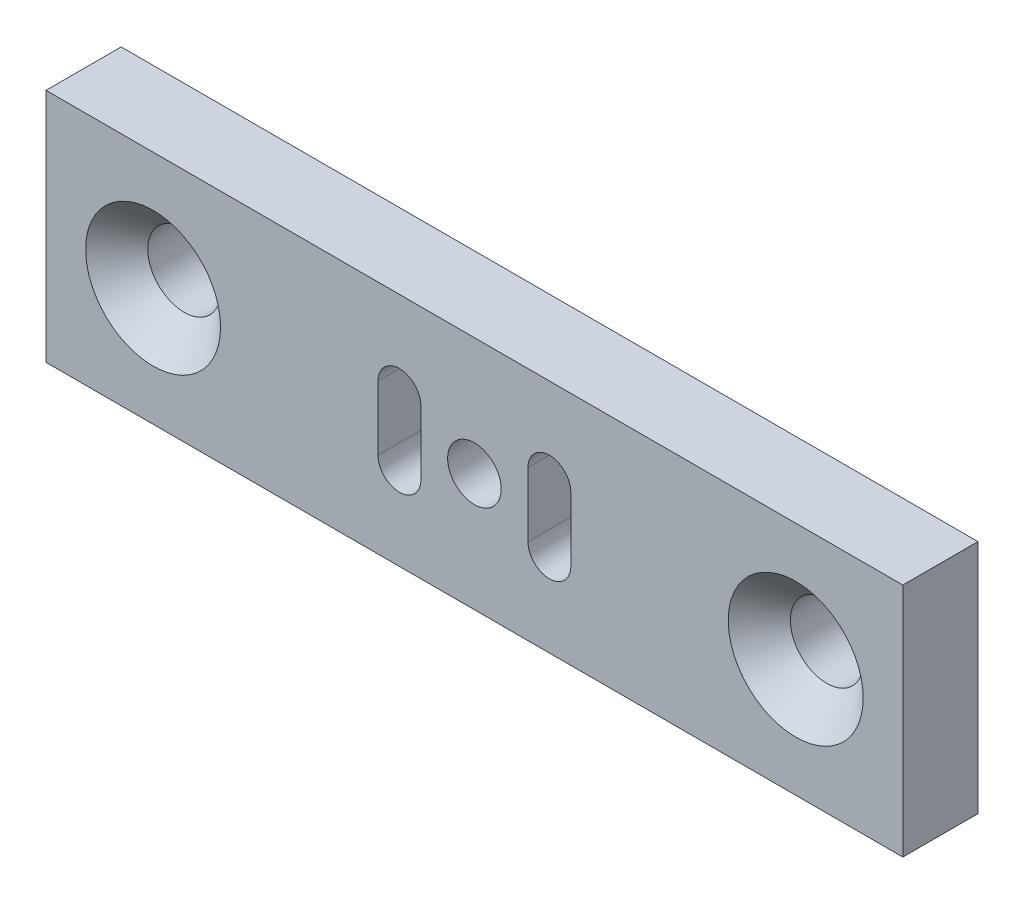
SolidWorks part; units mm, degrees
ref_plane "Plan de face" through (0, 0, 0) normal (0, 0, 1) x (1, 0, 0)
ref_plane "Plan de dessus" through (0, 0, 0) normal (0, 1, 0) x (1, 0, 0)
ref_plane "Plan de droite" through (0, 0, 0) normal (1, 0, 0) x (0, 0, -1)
sketch "Esquisse1" plane through (0, 0, 0) normal (0, 0, 1) x (1, 0, 0)
  line L0 (-2.625, 3.0182) -> (-2.625, -3.0182) construction
  line L1 (2.625, 3.0182) -> (-2.625, 3.0182) construction
  line L2 (2.625, 3.0182) -> (2.625, -3.0182) construction
  line L3 (2.625, -3.0182) -> (-2.625, -3.0182) construction
  line L5 (2.625, 3.0182) -> (-2.625, -3.0182) construction
  line L6 (2.625, -3.0182) -> (-2.625, 3.0182) construction
  line L8 (-4.341, -1.1938) -> (-20, -5.5) construction
  line L9 (20, -5.5) -> (-20, -5.5)
  line L10 (20, -5.5) -> (20, 5.5)
  line L11 (20, 5.5) -> (-20, 5.5)
  line L12 (-20, -5.5) -> (-20, 5.5)
  line L13 (20, -5.5) -> (-20, 5.5) construction
  line L14 (20, 5.5) -> (0, 0) construction
  circle A0 centre (0, 0) radius 4
  point P0 (0, 0)
  point P12 (0, 0)
  dimension "D2" = 8
  dimension "D1" = 5.25
  dimension "D5" = 40
  dimension "D6" = 11
extrude "Boss.-Extru.1" add sketch "Esquisse1" along normal blind 9.51
hole_wizard "Chambrage pour vis à tête ronde bombée M31" positions "Esquisse3D3" profile "Esquisse4" counterbore size "M3" standard "Ansi Metric"
sketch3d "Esquisse3D3"
  line L0 (15, 5.5, 9.51) -> (15, 5.5, 0) construction
  line L1 (15, 5.5, 9.51) -> (-15, 5.5, 9.51) construction
  line L2 (-15, 5.5, 9.51) -> (-15, 5.5, 0) construction
  point P0 (10, 5.5, 7.01)
  point P2 (-10, 5.5, 7.01)
  dimension "D1" = 5
  dimension "D2" = 2.5
  dimension "D3" = 2.5
  dimension "D4" = 5
sketch "Esquisse4" plane through (10, 5.5, 7.01) normal (1, 0, 0) x (0, 0, 1)
  line L0 (0, 0) -> (0, 11)
  line L1 (0, 11) -> (1.7, 11)
  line L3 (1.7, 11) -> (1.7, 2.4)
  line L4 (1.7, 2.4) -> (3.5, 2.4)
  line L5 (3.5, 2.4) -> (3.5, 0)
  line L7 (3.5, 0) -> (0, 0)
  line L11 (0, -6.35) -> (0, 107.95) construction
  dimension "Diamètre du perçage jusqu'au prochain" = 3.4
  dimension "Profondeur du perçage jusqu'au prochain" = 11
  dimension "Diamètre du chambrage" = 7
  dimension "Profondeur du chambrage" = 2.4
thread "Filetage2" pitch 0.45 start angle 0, offset 0, length 20, pitch 0.45, diameter 2.4
ref_plane "Plan3" through (5.3, 5.5, 4.51) normal (0, 0, 1) x (-1, 0, 0)
sketch "Profil de filetage3" plane through (5.3, 5.5, 4.51) normal (0, 0, 1) x (-1, 0, 0)
  line L0 (0, 0) -> (0, 0.45) construction
  line L1 (0, 0) -> (0.2436, 0.1406)
  line L2 (0.2436, 0.1406) -> (0.2436, 0.1969)
  line L3 (0.2436, 0.1969) -> (0, 0.3375)
  line L4 (0.2436, 0.1687) -> (0, 0.1687) construction
  line L11 (0, 0) -> (0, 0.3375)
  point P2 (0, 0)
  dimension "Pitch" = 0.45
  dimension "Profile_Angle" = 60
  dimension "Profile_Land" = 0.0562
  dimension "Profile_Height" = 0.2436
thread "Filetage3" pitch 0.45 start angle 0, offset 0, length 20, pitch 0.45, diameter 2.4
ref_plane "Plan4" through (-7.7, 5.5, 4.51) normal (0, 0, 1) x (-1, 0, 0)
sketch "Profil de filetage4" plane through (-7.7, 5.5, 4.51) normal (0, 0, 1) x (-1, 0, 0)
  line L0 (0, 0) -> (0, 0.45) construction
  line L1 (0, 0) -> (0.2436, 0.1406)
  line L2 (0.2436, 0.1406) -> (0.2436, 0.1969)
  line L3 (0.2436, 0.1969) -> (0, 0.3375)
  line L4 (0.2436, 0.1687) -> (0, 0.1687) construction
  line L11 (0, 0) -> (0, 0.3375)
  point P2 (0, 0)
  dimension "Pitch" = 0.45
  dimension "Profile_Angle" = 60
  dimension "Profile_Land" = 0.0562
  dimension "Profile_Height" = 0.2436
sketch "Esquisse16" plane through (0, 0, 9.51) normal (0, 0, 1) x (1, 0, 0)
  line L1 (-20, 5.5) -> (20, 5.5)
  line L2 (-20, 5.5) -> (-20, -5.5)
  line L3 (-20, -5.5) -> (20, -5.5)
  line L4 (20, 5.5) -> (20, -5.5)
extrude "Boss.-Extru.2" add sketch "Esquisse16" along normal blind 7
hole_wizard "Dégagement M32" positions "Esquisse17" profile "Esquisse18" hole size "M3" standard "Ansi Metric" end condition through all
sketch "Esquisse17" plane through (0, 0, 16.51) normal (0, 0, 1) x (1, 0, 0)
  point P0 (0, 0)
sketch "Esquisse18" plane through (0, 0, 16.51) normal (1, 0, 0) x (0, -1, 0)
  line L0 (0, 0) -> (0, 16.51)
  line L1 (0, 16.51) -> (1.25, 16.51)
  line L2 (1.25, 16.51) -> (1.25, 0)
  line L5 (1.25, 0) -> (0, 0)
  line L11 (0, -6.35) -> (0, 107.95) construction
  dimension "Diamètre du perçage jusqu'au prochain" = 2.5
  dimension "Profondeur du perçage jusqu'au prochain" = 16.51
sketch "Esquisse19" plane through (0, 0, 16.51) normal (0, 0, 1) x (1, 0, 0)
  line L0 (-3.5, 1.5) -> (-3.5, -1.5) construction
  line L1 (-2.5, 1.5) -> (-2.5, -1.5)
  line L2 (-4.5, 1.5) -> (-4.5, -1.5)
  line L3 (3.5, 1.5) -> (3.5, -1.5) construction
  line L4 (4.5, 1.5) -> (4.5, -1.5)
  line L5 (2.5, 1.5) -> (2.5, -1.5)
  arc A0 (-2.5, 1.5) -> (-4.5, 1.5) centre (-3.5, 1.5) ccw
  arc A1 (-4.5, -1.5) -> (-2.5, -1.5) centre (-3.5, -1.5) ccw
  arc A3 (4.5, 1.5) -> (2.5, 1.5) centre (3.5, 1.5) ccw
  arc A4 (2.5, -1.5) -> (4.5, -1.5) centre (3.5, -1.5) ccw
  circle A5 centre (0, 0) radius 1.25 construction
  point P2 (-3.5, 0)
  point P7 (3.5, 0)
  dimension "D5" = 3.5
  dimension "D3" = 3
  dimension "D6" = 3.5
  dimension "D8" = 5.5
  dimension "D1" = 1
  dimension "D2" = 1
  dimension "D4" = 3
  dimension "D7" = 5.5
extrude "Enlèv. mat.-Extru.1" cut sketch "Esquisse19" against normal blind 7
thread "Filetage4" pitch 0.5 start angle 0, offset 0, length 20, pitch 0.5, diameter 3.4
ref_plane "Plan5" through (-1.7, 0, 14.51) normal (0, -1, 0) x (-1, 0, 0)
sketch "Profil de filetage5" plane through (-1.7, 0, 14.51) normal (0, -1, 0) x (-1, 0, 0)
  line L0 (0, 0) -> (0, 0.5) construction
  line L1 (0, 0) -> (0.2706, 0.1562)
  line L2 (0.2706, 0.1562) -> (0.2706, 0.2187)
  line L3 (0.2706, 0.2187) -> (0, 0.375)
  line L4 (0.2706, 0.1875) -> (0, 0.1875) construction
  line L11 (0, 0) -> (0, 0.375)
  point P2 (0, 0)
  dimension "Pitch" = 0.5
  dimension "Profile_Angle" = 60
  dimension "Profile_Land" = 0.0625
  dimension "Profile_Height" = 0.2706
hole_wizard "Chambrage pour vis à tête ronde bombée M32" positions "Esquisse22" profile "Esquisse23" counterbore size "M3" standard "Ansi Metric" end condition through all
sketch "Esquisse22" plane through (0, 5.5, 0) normal (0, 1, 0) x (1, 0, 0)
  point P0 (14, -6.51)
  point P2 (-14, -6.51)
  dimension "D1" = 10
  dimension "D2" = 10
  dimension "D3" = 6
  dimension "D4" = 6
sketch "Esquisse23" plane through (14, 5.5, 6.51) normal (1, 0, 0) x (0, 0, 1)
  line L0 (0, 0) -> (0, 11)
  line L1 (0, 11) -> (1.7, 11)
  line L3 (1.7, 11) -> (1.7, 2.4)
  line L4 (1.7, 2.4) -> (3, 2.4)
  line L5 (3, 2.4) -> (3, 0)
  line L7 (3, 0) -> (0, 0)
  line L11 (0, -6.35) -> (0, 107.95) construction
  dimension "Diamètre du perçage jusqu'au prochain" = 3.4
  dimension "Profondeur du perçage jusqu'au prochain" = 11
  dimension "Diamètre du chambrage" = 6
  dimension "Profondeur du chambrage" = 2.4
sketch "Esquisse24" plane through (0, 0, 0) normal (0, 0, -1) x (-1, 0, 0)
  line L1 (20, -5.5) -> (-20, -5.5)
  line L2 (20, -5.5) -> (20, 5.5)
  line L3 (20, 5.5) -> (-20, 5.5)
  line L4 (-20, -5.5) -> (-20, 5.5)
  line L5 (20, -5.5) -> (-20, 5.5) construction
  line L6 (20, 5.5) -> (-20, -5.5) construction
  point P0 (0, 0)
extrude "Boss.-Extru.3" [suppressed] add sketch "Esquisse24" along normal blind 1
sketch "Esquisse25" [suppressed] plane through (0, 0, -1) normal (0, 0, -1) x (-1, 0, 0)
  line L0 (-2.625, 2.625) -> (-2.625, -2.625) construction
  line L1 (2.625, 2.625) -> (-2.625, 2.625) construction
  line L2 (2.625, 2.625) -> (2.625, -2.625) construction
  line L3 (2.625, -2.625) -> (-2.625, -2.625) construction
  line L4 (2.625, 2.625) -> (-2.625, -2.625) construction
  line L5 (2.625, -2.625) -> (-2.625, 2.625) construction
  line L6 (-4.227, -1.5499) -> (-14.4118, -5.2843) construction
  line L7 (14.4118, -5.2843) -> (-14.4118, -5.2843) construction
  line L8 (14.4118, -5.2843) -> (14.4118, 5.2843) construction
  line L9 (14.4118, 5.2843) -> (-14.4118, 5.2843) construction
  line L10 (-14.4118, -5.2843) -> (-14.4118, 5.2843) construction
  line L11 (14.4118, -5.2843) -> (-14.4118, 5.2843) construction
  line L12 (14.4118, 5.2843) -> (0, 0) construction
  circle A0 centre (0, 0) radius 3.7123
  point P0 (0, 0)
  point P7 (0, 0)
extrude "Enlèv. mat.-Extru.3" [suppressed] cut sketch "Esquisse25" against normal blind 3.5
hole_wizard "Fraisage pour vis à tête fraisée M31" positions "Esquisse31" profile "Esquisse32" countersink size "M3" standard "Ansi Metric"
sketch "Esquisse31" plane through (0, 0, 16.51) normal (0, 0, 1) x (1, 0, 0)
  point P0 (-15, 0)
  point P2 (15, 0)
  dimension "D1" = 5.5
  dimension "D2" = 5
  dimension "D3" = 5
  dimension "D4" = 5.5
sketch "Esquisse32" plane through (-15, 0, 16.51) normal (1, 0, 0) x (0, -1, 0)
  line L0 (0, 0) -> (0, 7.0215)
  line L1 (0, 7.0215) -> (1.7, 6)
  line L2 (1.7, 6) -> (1.7, 1.45)
  line L3 (1.7, 1.45) -> (3.15, 0)
  line L5 (3.15, 0) -> (0, 0)
  line L6 (-1.7, 1.45) -> (-3.15, 0) construction
  line L10 (0, 7.0215) -> (-1.7, 6) construction
  line L11 (0, -6.35) -> (0, 107.95) construction
  dimension "Diamètre du perçage" = 3.4
  dimension "Profondeur du perçage" = 6
  dimension "Diamètre du fraisage entrant" = 6.3
  dimension "Angle du fraisage entrant" = 90
  dimension "Angle de pointe" = 118
sketch "Esquisse33" plane through (0, 0, 0) normal (0, 0, -1) x (-1, 0, 0)
  line L1 (26.8087, -15.7158) -> (-26.8087, -15.7158)
  line L2 (26.8087, -15.7158) -> (26.8087, 15.7158)
  line L3 (26.8087, 15.7158) -> (-26.8087, 15.7158)
  line L4 (-26.8087, -15.7158) -> (-26.8087, 15.7158)
  line L5 (26.8087, -15.7158) -> (-26.8087, 15.7158) construction
  line L6 (26.8087, 15.7158) -> (-26.8087, -15.7158) construction
  point P0 (0, 0)
extrude "Enlèv. mat.-Extru.4" cut sketch "Esquisse33" against normal blind 13
